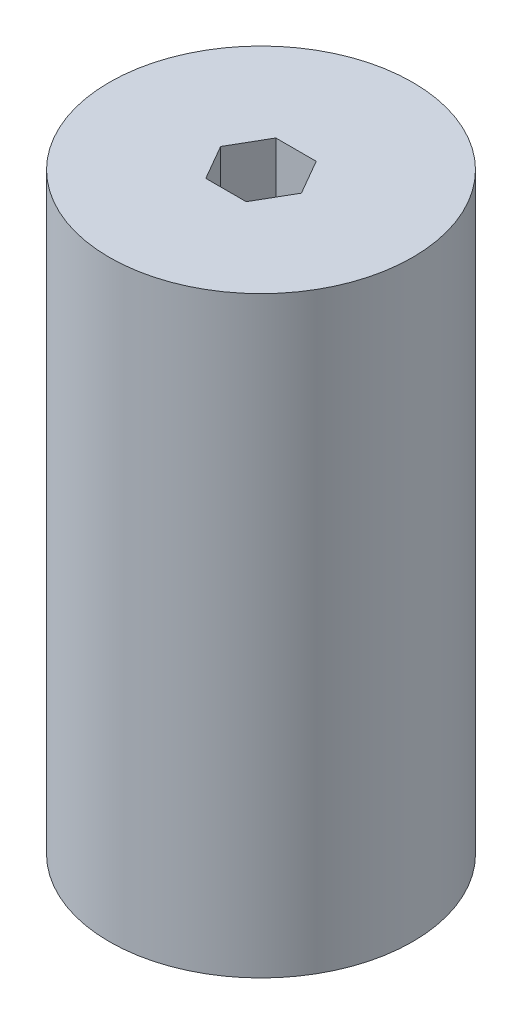
SolidWorks part; units mm, degrees
ref_plane "Front Plane" through (0, 0, 0) normal (0, 0, 1) x (1, 0, 0)
ref_plane "Top Plane" through (0, 0, 0) normal (0, 1, 0) x (1, 0, 0)
ref_plane "Right Plane" through (0, 0, 0) normal (1, 0, 0) x (0, 0, -1)
sketch "Sketch1" plane through (0, 0, 0) normal (0, 1, 0) x (1, 0, 0)
  line L1 (8.6603, 0) -> (4.3301, 7.5)
  line L2 (4.3301, 7.5) -> (-4.3301, 7.5)
  line L3 (-4.3301, 7.5) -> (-8.6603, 0)
  line L4 (-8.6603, 0) -> (-4.3301, -7.5)
  line L5 (-4.3301, -7.5) -> (4.3301, -7.5)
  line L6 (4.3301, -7.5) -> (8.6603, 0)
  circle A0 centre (0, 0) radius 7.5 construction
  circle A1 centre (0, 0) radius 32.5
  dimension "D1" = 65
  dimension "D2" = 15
extrude "Boss-Extrude1" add sketch "Sketch1" along normal blind 127
